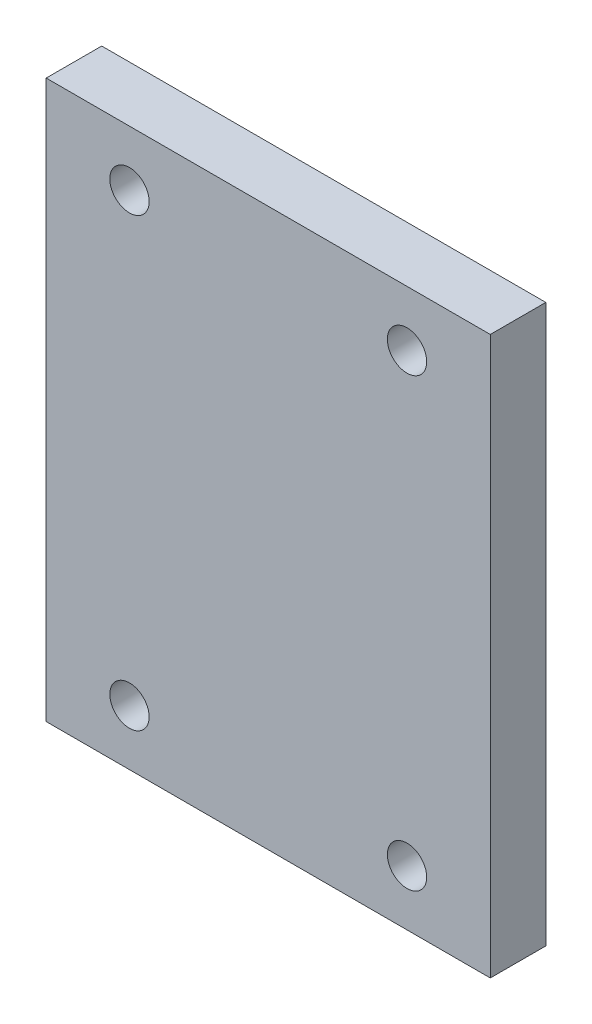
SolidWorks part; units mm, degrees
ref_plane "Front Plane" through (0, 0, 0) normal (0, 0, 1) x (1, 0, 0)
ref_plane "Top Plane" through (0, 0, 0) normal (0, 1, 0) x (1, 0, 0)
ref_plane "Right Plane" through (0, 0, 0) normal (1, 0, 0) x (0, 0, -1)
sketch "Sketch1" plane through (0, 0, 0) normal (0, 0, 1) x (1, 0, 0)
  line L1 (25.4, -31.877) -> (-25.4, -31.877)
  line L2 (25.4, -31.877) -> (25.4, 31.877)
  line L3 (25.4, 31.877) -> (-25.4, 31.877)
  line L4 (-25.4, -31.877) -> (-25.4, 31.877)
  line L5 (25.4, -31.877) -> (-25.4, 31.877) construction
  line L6 (25.4, 31.877) -> (-25.4, -31.877) construction
  point P0 (0, 0)
  dimension "D1" = 63.754
  dimension "D2" = 50.8
extrude "Boss-Extrude1" add sketch "Sketch1" along normal blind 6.35
hole_wizard "M4 Clearance Hole1" positions "Sketch2" profile "Sketch3" hole size "M4" standard "ANSI Metric" end condition through all
sketch "Sketch2" plane through (0, 0, 0) normal (0, 0, -1) x (-1, 0, 0)
  point P0 (-15.875, 25.527)
  point P3 (15.875, 25.527)
  point P6 (15.875, -25.527)
  point P9 (-15.875, -25.527)
sketch "Sketch3" plane through (15.875, 25.527, 0) normal (1, 0, 0) x (0, 1, 0)
  line L0 (0, 0) -> (0, 6.35)
  line L1 (0, 6.35) -> (2.25, 6.35)
  line L2 (2.25, 6.35) -> (2.25, 0)
  line L5 (2.25, 0) -> (0, 0)
  line L11 (0, -6.35) -> (0, 107.95) construction
  dimension "Thru Hole Dia." = 4.5
  dimension "Thru Hole Depth" = 6.35
